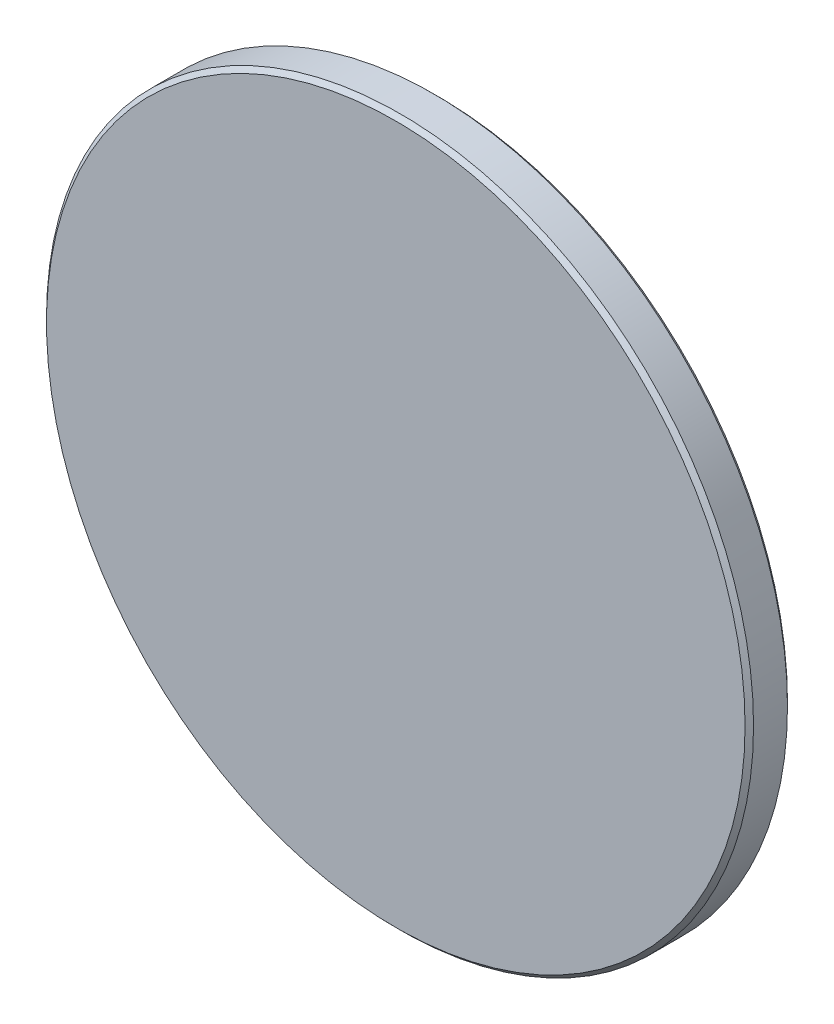
SolidWorks part; units mm, degrees
ref_plane "前视基准面" through (0, 0, 0) normal (0, 0, 1) x (1, 0, 0)
ref_plane "上视基准面" through (0, 0, 0) normal (0, 1, 0) x (1, 0, 0)
ref_plane "右视基准面" through (0, 0, 0) normal (1, 0, 0) x (0, 0, -1)
sketch "草图1" plane through (0, 0, 0) normal (0, 0, 1) x (1, 0, 0)
  circle A0 centre (0, 0) radius 25
  dimension "D1" = 50
extrude "凸台-拉伸1" add sketch "草图1" along normal blind 3
chamfer "倒角1" distance 0.3 angle 45 2 edges at (25, 0, 0) (25, 0, 3)
